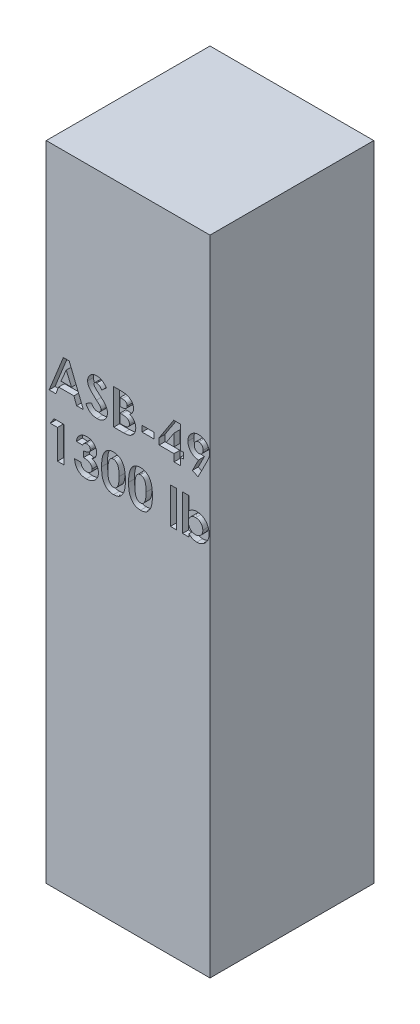
SolidWorks part; units mm, degrees
ref_plane "Front Plane" through (0, 0, 0) normal (0, 0, 1) x (1, 0, 0)
ref_plane "Top Plane" through (0, 0, 0) normal (0, 1, 0) x (1, 0, 0)
ref_plane "Right Plane" through (0, 0, 0) normal (1, 0, 0) x (0, 0, -1)
sketch "Sketch1" plane through (0, 0, 0) normal (0, 0, 1) x (1, 0, 0)
  line L1 (177.8, 698.5) -> (-177.8, 698.5)
  line L2 (177.8, 698.5) -> (177.8, -698.5)
  line L3 (177.8, -698.5) -> (-177.8, -698.5)
  line L4 (-177.8, 698.5) -> (-177.8, -698.5)
  line L5 (177.8, 698.5) -> (-177.8, -698.5) construction
  line L6 (177.8, -698.5) -> (-177.8, 698.5) construction
  point P0 (0, 0)
  dimension "D1" = 1397
  dimension "D2" = 355.6
extrude "Boss-Extrude1" add sketch "Sketch1" along normal blind 355.6
sketch "Sketch2" plane through (0, 0, 355.6) normal (0, 0, 1) x (1, 0, 0)
  line L0 (-177.8, 232.8333) -> (177.8, 232.8333) construction
  line L1 (-177.8, 698.5) -> (-177.8, -698.5) construction
  line L2 (177.8, -698.5) -> (177.8, 698.5) construction
  line L3 (177.8, 698.5) -> (-177.8, 698.5) construction
  text T0 "<b>ASB-49</b>\r\n<b>1300 lb</b>" font "Century Gothic" height 76.2
  dimension "D1" = 465.6667
extrude "Cut-Extrude1" cut sketch "Sketch2" against normal blind 12.7
